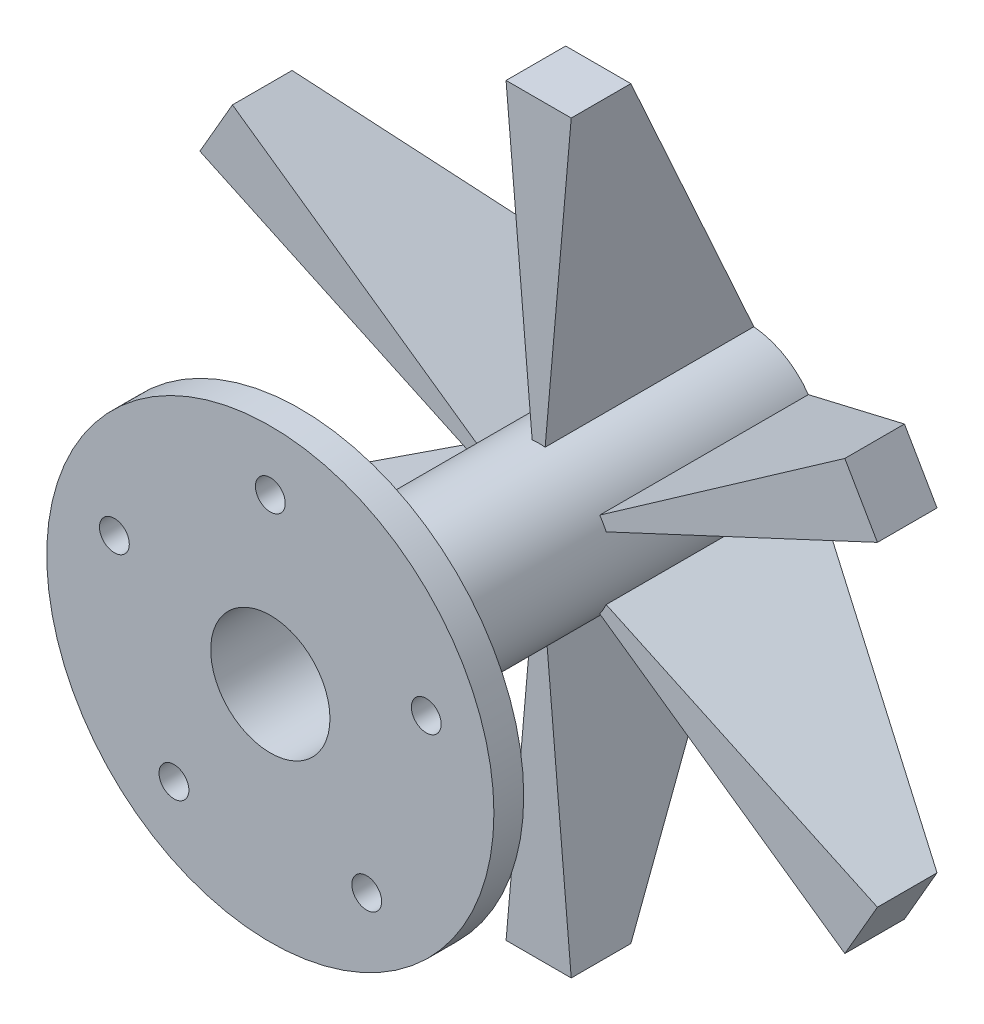
SolidWorks part; units mm, degrees
ref_plane "Front Plane" through (0, 0, 0) normal (0, 0, 1) x (1, 0, 0)
ref_plane "Top Plane" through (0, 0, 0) normal (0, 1, 0) x (1, 0, 0)
ref_plane "Right Plane" through (0, 0, 0) normal (1, 0, 0) x (0, 0, -1)
sketch "Sketch1" plane through (0, 0, 0) normal (0, 0, 1) x (1, 0, 0)
  circle A0 centre (0, 0) radius 75
  circle A1 centre (0, 0) radius 55 construction
  circle A2 centre (0, 55) radius 5
  circle A3 centre (52.3081, 16.9959) radius 5
  circle A4 centre (32.3282, -44.4959) radius 5
  circle A5 centre (-32.3282, -44.4959) radius 5
  circle A6 centre (-52.3081, 16.9959) radius 5
  point P16 (0, 0)
  dimension "D1" = 150
  dimension "D2" = 110
  dimension "D3" = 10
  dimension "D4" = 5
extrude "Boss-Extrude1" add sketch "Sketch1" along normal blind 10
sketch "Sketch2" plane through (0, 0, 0) normal (0, 0, -1) x (-1, 0, 0)
  circle A0 centre (0, 0) radius 25
  dimension "D1" = 50
extrude "Boss-Extrude2" add sketch "Sketch2" along normal blind 150
sketch "Sketch3" plane through (0, 0, -150) normal (0, 0, -1) x (-1, 0, 0)
  line L0 (0, 137.9757) -> (0, -133.6278) construction
  line L1 (-231.5052, 0) -> (193.575, 0) construction
  line L2 (2.1789, 24.9049) -> (10.9278, 124.9049)
  line L3 (-2.1789, 24.9049) -> (-10.9278, 124.9049)
  line L4 (-10.9278, 124.9049) -> (10.9278, 124.9049)
  circle A0 centre (0, 0) radius 25 construction
  circle A1 centre (0, 0) radius 25
  circle M4 centre (0, 0) radius 25
  dimension "D1" = 5
  dimension "D2" = 10
  dimension "D4" = 100
extrude "Boss-Extrude3" add sketch "Sketch3" against normal blind 70 contours L4 L3 L2 M4
chamfer "Chamfer2" distance 100 distance2 50 1 edges at (0, 124.9049, -150)
pattern_circular "CirPattern3" count 6 over 360 about axis through (0, 0, 0) along (0, 0, 1) of "Chamfer2", "Boss-Extrude3"
sketch "Sketch4" plane through (0, 0, 10) normal (0, 0, 1) x (1, 0, 0)
  circle A0 centre (0, 0) radius 20
  dimension "D1" = 40
extrude "Cut-Extrude1" cut sketch "Sketch4" against normal through all both and the other way through all
